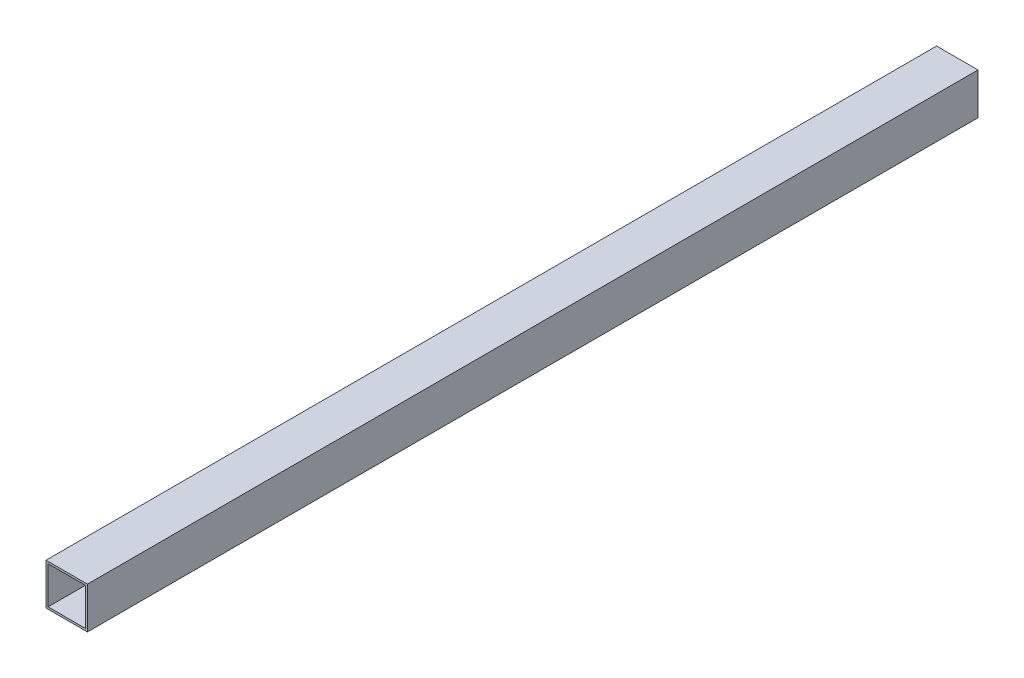
SolidWorks part; units mm, degrees
ref_plane "Front Plane" through (0, 0, 0) normal (0, 0, 1) x (1, 0, 0)
ref_plane "Top Plane" through (0, 0, 0) normal (0, 1, 0) x (1, 0, 0)
ref_plane "Right Plane" through (0, 0, 0) normal (1, 0, 0) x (0, 0, -1)
sketch "Sketch1" plane through (0, 0, 0) normal (0, 0, 1) x (1, 0, 0)
  line L1 (0, 0) -> (20, 0)
  line L2 (0, 0) -> (0, -20)
  line L3 (0, -20) -> (20, -20)
  line L4 (20, 0) -> (20, -20)
  line L5 (1, -19) -> (19, -19)
  line L6 (1, -19) -> (1, -1)
  line L7 (1, -1) -> (19, -1)
  line L8 (19, -19) -> (19, -1)
  line L9 (1, -19) -> (19, -1) construction
  line L10 (1, -1) -> (19, -19) construction
  point P5 (10, -10)
  dimension "D1" = 20
  dimension "D2" = 20
  dimension "D3" = 1
  dimension "D4" = 1
  dimension "D5" = 1
  dimension "D6" = 1
extrude "Boss-Extrude1" add sketch "Sketch1" along normal blind 430
